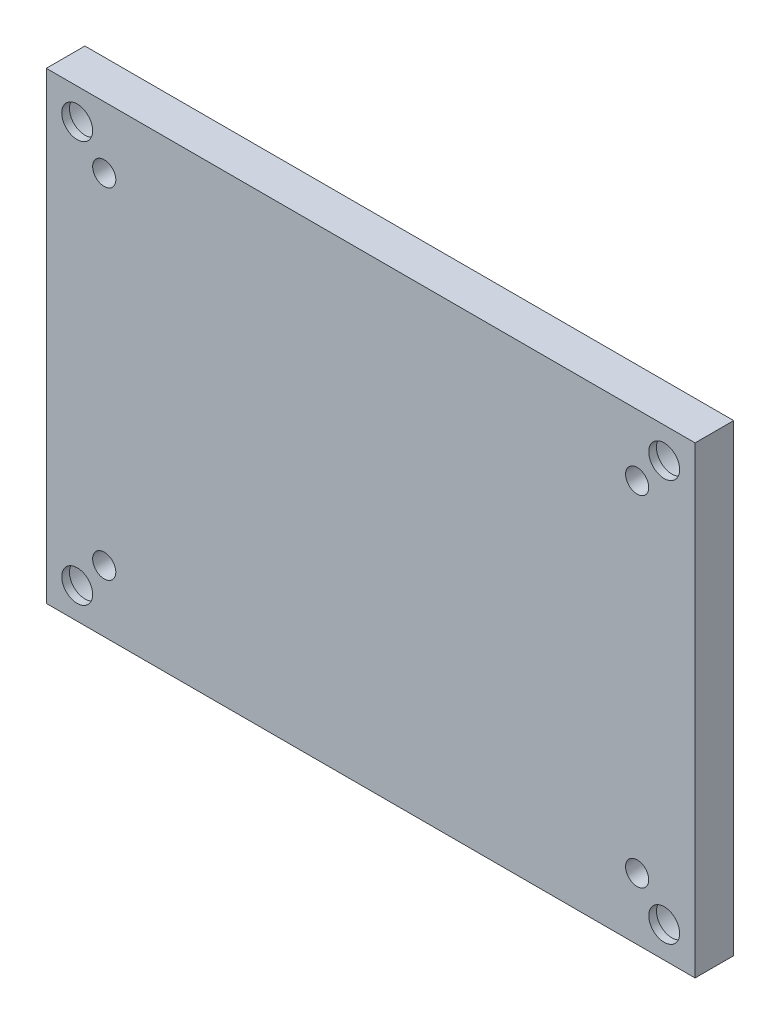
SolidWorks part; units mm, degrees
ref_plane "Front Plane" through (0, 0, 0) normal (0, 0, 1) x (1, 0, 0)
ref_plane "Top Plane" through (0, 0, 0) normal (0, 1, 0) x (1, 0, 0)
ref_plane "Right Plane" through (0, 0, 0) normal (1, 0, 0) x (0, 0, -1)
sketch "Sketch1" plane through (0, 0, 0) normal (0, 0, 1) x (1, 0, 0)
  line L0 (-39, 30) -> (-42, 30)
  line L1 (-39, -30) -> (39, -30)
  line L2 (-42, -27) -> (-42, 27)
  line L3 (-39, 30) -> (39, 30)
  line L4 (42, -27) -> (42, 27)
  line L5 (-42, 30) -> (-42, 27)
  line L6 (39, 30) -> (42, 30)
  line L7 (42, 30) -> (42, 27)
  line L8 (39, -30) -> (42, -30)
  line L9 (42, -30) -> (42, -27)
  line L10 (-42, -27) -> (-42, -30)
  line L11 (-42, -30) -> (-39, -30)
  point P0 (0, 0)
extrude "Boss-Extrude1" add sketch "Sketch1" along normal blind 5
sketch "Sketch2" plane through (0, 0, 0) normal (0, 0, -1) x (-1, 0, 0)
  circle A4 centre (38, 26) radius 3.5
  circle A5 centre (-38, 26) radius 3.5
  circle A6 centre (-38, -26) radius 3.5
  circle A7 centre (38, -26) radius 3.5
extrude "Cut-Extrude1" cut sketch "Sketch2" against normal blind 4
sketch "Sketch6" plane through (0, 0, 0) normal (0, 0, -1) x (-1, 0, 0)
  circle A0 centre (-38, 26) radius 2
  circle A1 centre (38, 26) radius 2
  circle A2 centre (38, -26) radius 2
  circle A3 centre (-38, -26) radius 2
extrude "Cut-Extrude2" cut sketch "Sketch6" against normal up to surface (5 mm away) up to face at (0, 0, 5)
sketch "Sketch7" plane through (0, 0, 5) normal (0, 0, 1) x (1, 0, 0)
  circle A0 centre (-34.5, 22) radius 1.5
  circle A1 centre (34.5, 22) radius 1.5
  circle A2 centre (34.5, -22) radius 1.5
  circle A3 centre (-34.5, -22) radius 1.5
  point P0 (0, 0)
extrude "Cut-Extrude3" cut sketch "Sketch7" against normal blind 3
sketch "Sketch8" plane through (0, 0, 0) normal (0, 0, -1) x (-1, 0, 0)
  text T0 "MADE IN INDIA" font "BankGothic Md BT" height 4
extrude "Cut-Extrude4" cut sketch "Sketch8" against normal blind 1
